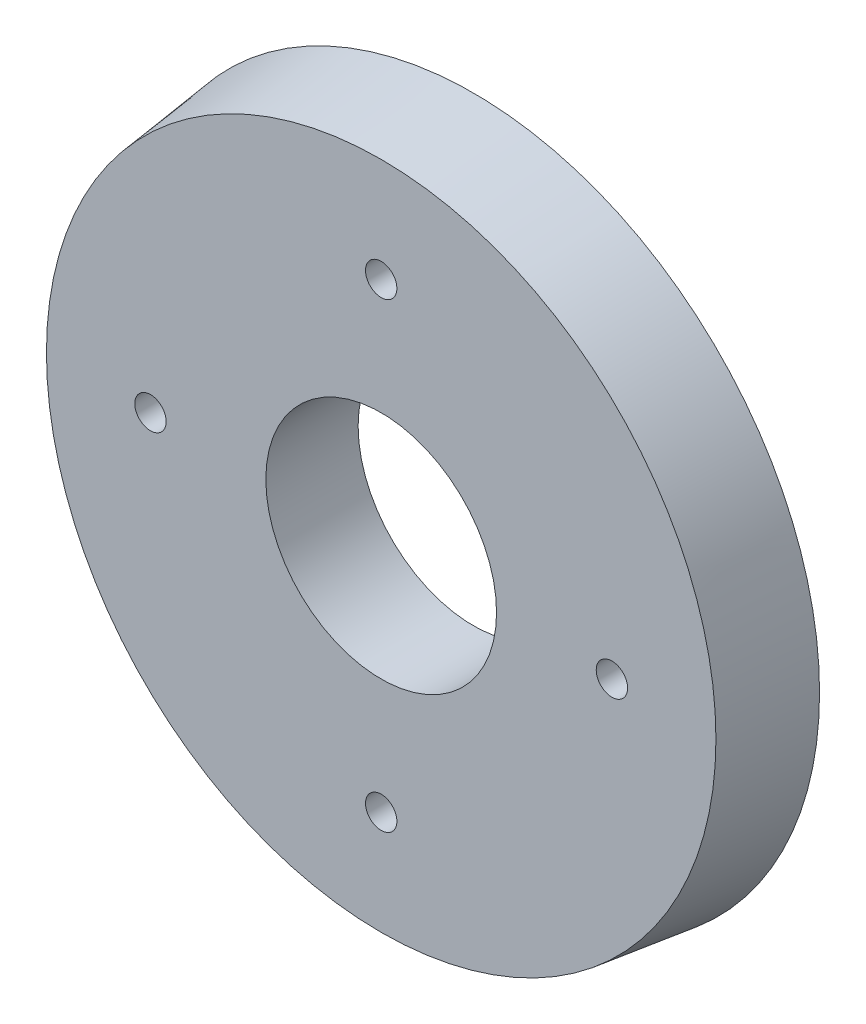
SolidWorks part; units mm, degrees
ref_plane "Front Plane" through (0, 0, 0) normal (0, 0, 1) x (1, 0, 0)
ref_plane "Top Plane" through (0, 0, 0) normal (0, 1, 0) x (1, 0, 0)
ref_plane "Right Plane" through (0, 0, 0) normal (1, 0, 0) x (0, 0, -1)
sketch "Sketch1" plane through (0, 0, 0) normal (0, 0, 1) x (1, 0, 0)
  line L0 (0, 0) -> (0, 92279.616) construction
  line L1 (0, 0) -> (-92279.616, 0) construction
  circle A0 centre (0, 0) radius 75
  dimension "D1" = 150
ref_plane "Plane1" through (0, 0, 20) normal (0, 0, 1) x (1, 0, 0)
extrude "Boss-Extrude1" add sketch "Sketch1" along normal blind 20 draft 7
sketch "Sketch6" plane through (0, 0, 0) normal (0, 0, -1) x (-1, 0, 0)
  circle A0 centre (0, 0) radius 25
  circle A1 centre (0, 0) radius 50 construction
  circle A2 centre (0, 50) radius 3.4
  circle A3 centre (50, 0) radius 3.4
  circle A4 centre (0, -50) radius 3.4
  circle A5 centre (-50, 0) radius 3.4
  point P15 (0, 0)
  dimension "D1" = 50
  dimension "D2" = 100
  dimension "D3" = 6.8
  dimension "D4" = 4
extrude "Cut-Extrude1" cut sketch "Sketch6" against normal through all
